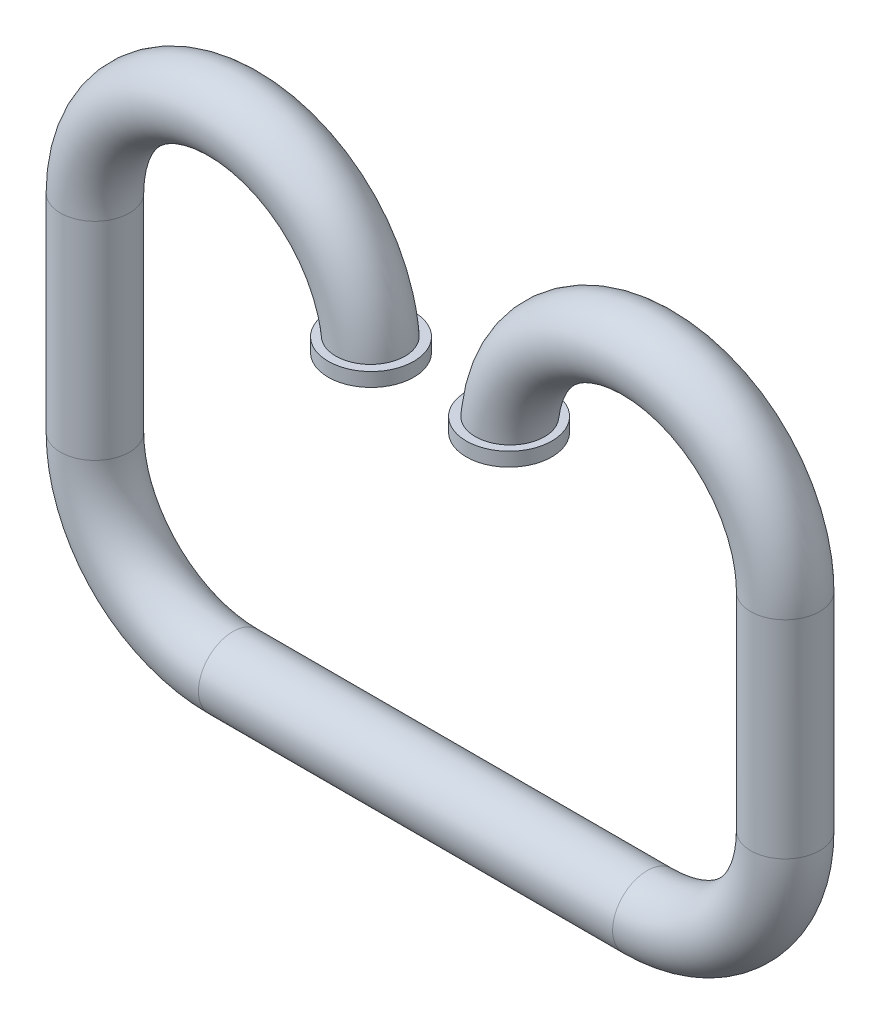
SolidWorks part; units mm, degrees
ref_plane "Front Plane" through (0, 0, 0) normal (0, 0, 1) x (1, 0, 0)
ref_plane "Top Plane" through (0, 0, 0) normal (0, 1, 0) x (1, 0, 0)
ref_plane "Right Plane" through (0, 0, 0) normal (1, 0, 0) x (0, 0, -1)
sketch "Sketch1" plane through (0, 0, 0) normal (0, 0, 1) x (1, 0, 0)
  line L0 (-2, 0) -> (-2, -1.5)
  line L1 (-1, -2.5) -> (0.5, -2.5)
  arc A0 (0, 0) -> (-2, 0) centre (-1, 0) ccw
  arc A1 (-2, -1.5) -> (-1, -2.5) centre (-1, -1.5) ccw
sketch "Sketch3" plane through (0, 0, 0) normal (0, 1, 0) x (1, 0, 0)
  circle A0 centre (0, 0) radius 0.2
sweep "Sweep-Thin1" add profiles "Sketch3" path "Sketch1" parameters "D1"=0.05
sketch "Sketch5" plane through (0, 0, 0) normal (0, 0, 1) x (1, 0, 0)
  line L0 (0, 0) -> (0, 0.1)
sketch "Sketch6" plane through (0, 0, 0) normal (0, 1, 0) x (1, 0, 0)
  circle A0 centre (0, 0) radius 0.21
sweep "Sweep-Thin2" add profiles "Sketch6" path "Sketch5" parameters "D1"=0.1
mirror "Mirror2" about plane through (0.5, -2.5, 0) normal (1, 0, 0) of bodies 102
